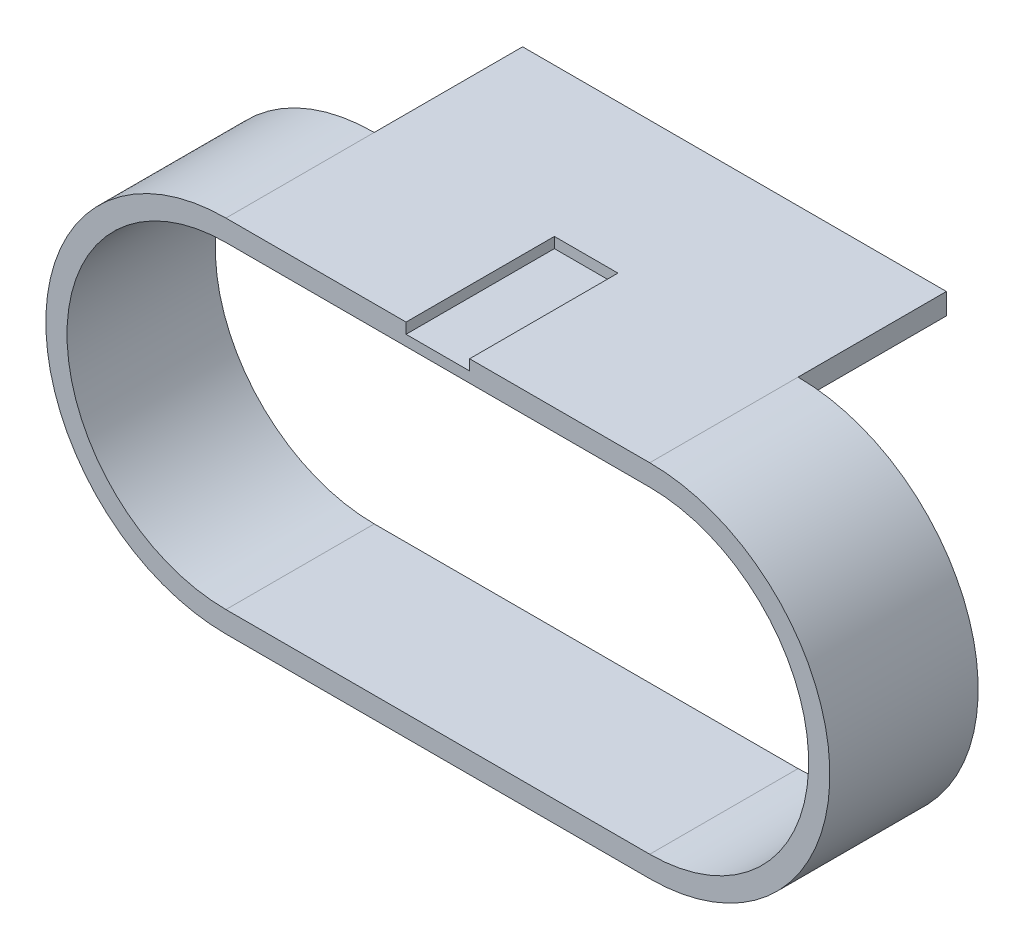
SolidWorks part; units mm, degrees
material "Thornel Mat VMA"
ref_plane "Front Plane" through (0, 0, 0) normal (0, 0, 1) x (1, 0, 0)
ref_plane "Top Plane" through (0, 0, 0) normal (0, 1, 0) x (1, 0, 0)
ref_plane "Right Plane" through (0, 0, 0) normal (1, 0, 0) x (0, 0, -1)
sketch "Sketch2" plane through (0, 0, 0) normal (0, 0, 1) x (1, 0, 0)
  line L0 (-25.4, 0) -> (25.4, 0) construction
  line L1 (-25.4, 19.05) -> (25.4, 19.05)
  line L2 (-25.4, -19.05) -> (25.4, -19.05)
  line L3 (-25.4, 21.59) -> (25.4, 21.59)
  line L4 (-25.4, -21.59) -> (25.4, -21.59)
  arc A0 (-25.4, 19.05) -> (-25.4, -19.05) centre (-25.4, 0) ccw
  arc A1 (25.4, -19.05) -> (25.4, 19.05) centre (25.4, 0) ccw
  arc A2 (25.4, -21.59) -> (25.4, 21.59) centre (25.4, 0) ccw
  arc A3 (-25.4, 21.59) -> (-25.4, -21.59) centre (-25.4, 0) ccw
  point P3 (0, 0)
  point P8 (0, 0)
  dimension "D1" = 19.05
  dimension "D2" = 50.8
  dimension "D3" = 2.54
extrude "Boss-Extrude1" add sketch "Sketch2" along normal mid plane 17.78
sketch "Sketch3" plane through (0, 0, 0) normal (0, 0, 1) x (1, 0, 0)
  line L0 (25.4, 21.59) -> (-25.4, 21.59) construction
  line L1 (-3.81, 20.32) -> (3.81, 20.32)
  line L2 (-3.81, 20.32) -> (-3.81, 22.86)
  line L3 (-3.81, 22.86) -> (3.81, 22.86)
  line L4 (3.81, 20.32) -> (3.81, 22.86)
  line L5 (-3.81, 20.32) -> (3.81, 22.86) construction
  line L6 (-3.81, 22.86) -> (3.81, 20.32) construction
  point P0 (0, 21.59)
  dimension "D1" = 2.54
  dimension "D2" = 7.62
extrude "Cut-Extrude1" cut sketch "Sketch3" against normal up to next and the other way up to next
sketch "Sketch4" plane through (0, 0, -8.89) normal (0, 0, -1) x (-1, 0, 0)
  line L0 (-25.4, 19.05) -> (25.4, 19.05) construction
  line L6 (-25.4, 19.05) -> (25.4, 19.05)
  line L12 (-25.4, 21.59) -> (-25.4, 19.05)
  line L13 (25.4, 21.59) -> (25.4, 19.05)
  line L14 (-25.4, 21.59) -> (25.4, 21.59)
  line L15 (-25.4, 21.59) -> (-3.81, 21.59) construction
extrude "Boss-Extrude2" add sketch "Sketch4" along normal blind 17.78
